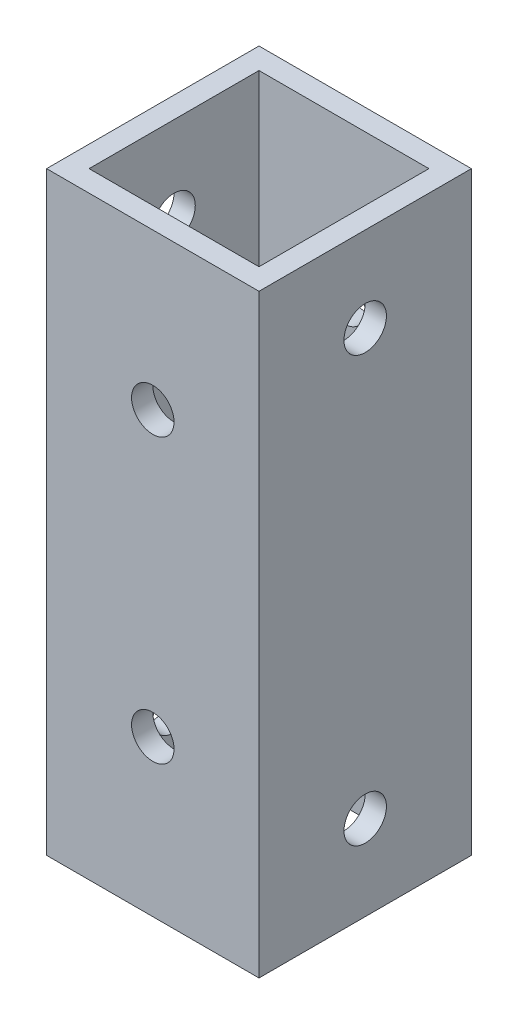
SolidWorks part; units mm, degrees
material "6061 Alloy"
ref_plane "Front Plane" through (0, 0, 0) normal (0, 0, 1) x (1, 0, 0)
ref_plane "Top Plane" through (0, 0, 0) normal (0, 1, 0) x (1, 0, 0)
ref_plane "Right Plane" through (0, 0, 0) normal (1, 0, 0) x (0, 0, -1)
sketch "Sketch1" plane through (0, 0, 0) normal (0, 1, 0) x (1, 0, 0)
  line L1 (0, 0) -> (15, 0)
  line L2 (0, 0) -> (0, 15)
  line L3 (0, 15) -> (15, 15)
  line L4 (15, 0) -> (15, 15)
  dimension "D1" = 15
extrude "Extrude-Thin1" add sketch "Sketch1" along normal blind 42 thin thin type one direction reverse wall 1.5
sketch "Sketch2" plane through (0, 0, 0) normal (-1, 0, 0) x (0, 0, 1)
  line L0 (-15, 0) -> (0, 0) construction
  line L1 (0, 42) -> (0, 0) construction
  circle A0 centre (-7.5, 36) radius 1.5
  circle A1 centre (-7.5, 6) radius 1.5
  dimension "D1" = 3
  dimension "D2" = 7.5
  dimension "D3" = 6
  dimension "D4" = 36
extrude "Cut-Extrude1" cut sketch "Sketch2" against normal through all
sketch "Sketch3" plane through (0, 0, -15) normal (0, 0, -1) x (-1, 0, 0)
  line L0 (-7.5, 42) -> (-7.5, 0) construction
  line L1 (-15, 42) -> (0, 42) construction
  line L2 (-15, 0) -> (0, 0) construction
  line L3 (-15, 21) -> (0, 21) construction
  line L4 (-15, 42) -> (-15, 0) construction
  line L5 (0, 42) -> (0, 0) construction
  circle A0 centre (-7.5, 31) radius 1.5
  circle A1 centre (-7.5, 11) radius 1.5
  dimension "D1" = 3
  dimension "D2" = 20
extrude "Cut-Extrude2" cut sketch "Sketch3" against normal through all
